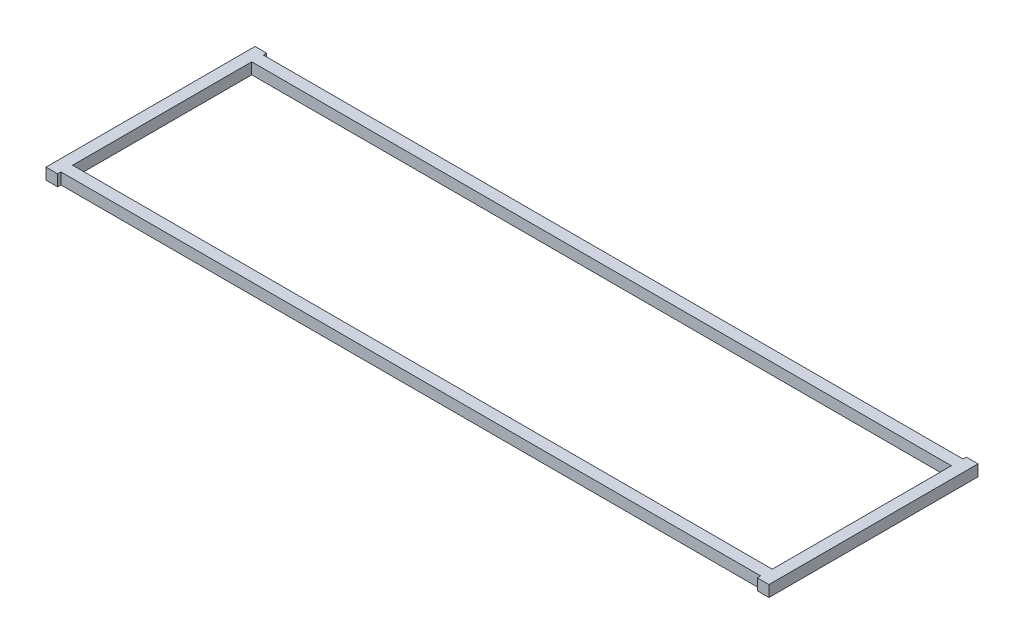
SolidWorks part; units mm, degrees
ref_plane "Front" through (0, 0, 0) normal (0, 0, 1) x (1, 0, 0)
ref_plane "Top" through (0, 0, 0) normal (0, 1, 0) x (1, 0, 0)
ref_plane "Right" through (0, 0, 0) normal (1, 0, 0) x (0, 0, -1)
sketch "Sketch1" plane through (0, 0, 0) normal (0, 1, 0) x (1, 0, 0)
  line L0 (196.85, 58.6835) -> (203.2, 58.6835)
  line L1 (-203.2, 58.6835) -> (-196.85, 58.6835)
  line L2 (-203.2, 58.6835) -> (-203.2, -58.6835)
  line L3 (-203.2, -58.6835) -> (-196.85, -58.6835)
  line L4 (203.2, 58.6835) -> (203.2, -58.6835)
  line L5 (-203.2, 58.6835) -> (203.2, -58.6835) construction
  line L6 (-203.2, -58.6835) -> (203.2, 58.6835) construction
  line L8 (-196.85, 58.6835) -> (-196.85, 56.8196)
  line L9 (-196.85, 56.8196) -> (196.85, 56.8196)
  line L10 (196.85, 58.6835) -> (196.85, 56.8196)
  line L12 (-196.85, -58.6835) -> (-196.85, -56.8196)
  line L13 (-196.85, -56.8196) -> (196.85, -56.8196)
  line L14 (196.85, -58.6835) -> (196.85, -56.8196)
  line L15 (196.85, -58.6835) -> (203.2, -58.6835)
  line L17 (-196.85, -50.4696) -> (196.85, -50.4696)
  line L18 (-196.85, -50.4696) -> (-196.85, 50.4696)
  line L19 (-196.85, 50.4696) -> (196.85, 50.4696)
  line L20 (196.85, -50.4696) -> (196.85, 50.4696)
  line L21 (-196.85, -50.4696) -> (196.85, 50.4696) construction
  line L22 (-196.85, 50.4696) -> (196.85, -50.4696) construction
  point P0 (0, 0)
  point P14 (0, 0)
  dimension "D1" = 406.4
  dimension "D2" = 117.3671
  dimension "D3" = 6.35
  dimension "D4" = 6.35
  dimension "D6" = 6.35
  dimension "D7" = 6.35
  dimension "D5" = 1.8639
extrude "Boss-Extrude1" add sketch "Sketch1" along normal blind 6.35
ref_plane "Plane1" through (0, 6.35, 0) normal (0, 1, 0) x (1, 0, 0)
sketch "Sketch2" plane through (0, 6.35, 0) normal (0, 1, 0) x (1, 0, 0)
  line L24 (196.7484, -58.7851) -> (203.3016, -58.7851)
  line L25 (203.3016, -58.7851) -> (203.3016, 58.7851)
  line L26 (203.3016, 58.7851) -> (196.7484, 58.7851)
  line L27 (196.7484, 58.7851) -> (196.7484, 56.9212)
  line L28 (196.7484, 56.9212) -> (-196.7484, 56.9212)
  line L29 (-196.7484, 56.9212) -> (-196.7484, 58.7851)
  line L30 (-196.7484, 58.7851) -> (-203.3016, 58.7851)
  line L31 (-203.3016, 58.7851) -> (-203.3016, -58.7851)
  line L32 (-203.3016, -58.7851) -> (-196.7484, -58.7851)
  line L33 (-196.7484, -58.7851) -> (-196.7484, -56.9212)
  line L34 (-196.7484, -56.9212) -> (196.7484, -56.9212)
  line L35 (196.7484, -56.9212) -> (196.7484, -58.7851)
  line L36 (196.7484, -58.7851) -> (203.3016, -58.7851)
  line L37 (203.3016, -58.7851) -> (203.3016, 58.7851)
  line L38 (203.3016, 58.7851) -> (196.7484, 58.7851)
  line L39 (196.7484, 58.7851) -> (196.7484, 56.9212)
  line L40 (196.7484, 56.9212) -> (-196.7484, 56.9212)
  line L41 (-196.7484, 56.9212) -> (-196.7484, 58.7851)
  line L42 (-196.7484, 58.7851) -> (-203.3016, 58.7851)
  line L43 (-203.3016, 58.7851) -> (-203.3016, -58.7851)
  line L44 (-203.3016, -58.7851) -> (-196.7484, -58.7851)
  line L45 (-196.7484, -58.7851) -> (-196.7484, -56.9212)
  line L46 (-196.7484, -56.9212) -> (196.7484, -56.9212)
  line L47 (196.7484, -56.9212) -> (196.7484, -58.7851)
  line L50 (196.7484, -50.368) -> (196.7484, 50.368)
  line L51 (-196.7484, -50.368) -> (196.7484, -50.368)
  line L52 (-196.7484, 50.368) -> (-196.7484, -50.368)
  line L53 (196.7484, 50.368) -> (-196.7484, 50.368)
  line L54 (196.7484, -50.368) -> (196.7484, 50.368)
  line L55 (-196.7484, -50.368) -> (196.7484, -50.368)
  line L56 (-196.7484, 50.368) -> (-196.7484, -50.368)
  line L57 (196.7484, 50.368) -> (-196.7484, 50.368)
  dimension "D1" = 0.1016
  dimension "D2" = 0.1016
extrude "Boss-Extrude2" add sketch "Sketch2" against normal blind 6.35
ref_plane "Plane2" [suppressed] through (0, 6.35, 0) normal (0, 1, 0) x (1, 0, 0)
sketch "Sketch3" [suppressed] plane through (0, 6.35, 0) normal (0, 1, 0) x (1, 0, 0)
  line L24 (196.7484, -63.354) -> (203.3016, -63.354)
  line L25 (203.3016, -63.354) -> (203.3016, 63.354)
  line L26 (203.3016, 63.354) -> (196.7484, 63.354)
  line L27 (196.7484, 63.354) -> (196.7484, 61.4901)
  line L28 (196.7484, 61.4901) -> (-196.7484, 61.4901)
  line L29 (-196.7484, 61.4901) -> (-196.7484, 63.354)
  line L30 (-196.7484, 63.354) -> (-203.3016, 63.354)
  line L31 (-203.3016, 63.354) -> (-203.3016, -63.354)
  line L32 (-203.3016, -63.354) -> (-196.7484, -63.354)
  line L33 (-196.7484, -63.354) -> (-196.7484, -61.4901)
  line L34 (-196.7484, -61.4901) -> (196.7484, -61.4901)
  line L35 (196.7484, -61.4901) -> (196.7484, -63.354)
  line L36 (196.7484, -63.354) -> (203.3016, -63.354)
  line L37 (203.3016, -63.354) -> (203.3016, 63.354)
  line L38 (203.3016, 63.354) -> (196.7484, 63.354)
  line L39 (196.7484, 63.354) -> (196.7484, 61.4901)
  line L40 (196.7484, 61.4901) -> (-196.7484, 61.4901)
  line L41 (-196.7484, 61.4901) -> (-196.7484, 63.354)
  line L42 (-196.7484, 63.354) -> (-203.3016, 63.354)
  line L43 (-203.3016, 63.354) -> (-203.3016, -63.354)
  line L44 (-203.3016, -63.354) -> (-196.7484, -63.354)
  line L45 (-196.7484, -63.354) -> (-196.7484, -61.4901)
  line L46 (-196.7484, -61.4901) -> (196.7484, -61.4901)
  line L47 (196.7484, -61.4901) -> (196.7484, -63.354)
  line L50 (196.7484, -54.9369) -> (196.7484, 54.9369)
  line L51 (-196.7484, -54.9369) -> (196.7484, -54.9369)
  line L52 (-196.7484, 54.9369) -> (-196.7484, -54.9369)
  line L53 (196.7484, 54.9369) -> (-196.7484, 54.9369)
  line L54 (196.7484, -54.9369) -> (196.7484, 54.9369)
  line L55 (-196.7484, -54.9369) -> (196.7484, -54.9369)
  line L56 (-196.7484, 54.9369) -> (-196.7484, -54.9369)
  line L57 (196.7484, 54.9369) -> (-196.7484, 54.9369)
  dimension "D1" = 0.1016
  dimension "D2" = 0.1016
extrude "Boss-Extrude3" [suppressed] add sketch "Sketch3" against normal blind 6.35
ref_plane "Plane3" [suppressed] through (0, 6.35, 0) normal (0, 1, 0) x (1, 0, 0)
sketch "Sketch4" [suppressed] plane through (0, 6.35, 0) normal (0, 1, 0) x (1, 0, 0)
  line L24 (196.7484, -67.9228) -> (203.3016, -67.9228)
  line L25 (203.3016, -67.9228) -> (203.3016, 67.9228)
  line L26 (203.3016, 67.9228) -> (196.7484, 67.9228)
  line L27 (196.7484, 67.9228) -> (196.7484, 66.0589)
  line L28 (196.7484, 66.0589) -> (-196.7484, 66.0589)
  line L29 (-196.7484, 66.0589) -> (-196.7484, 67.9228)
  line L30 (-196.7484, 67.9228) -> (-203.3016, 67.9228)
  line L31 (-203.3016, 67.9228) -> (-203.3016, -67.9228)
  line L32 (-203.3016, -67.9228) -> (-196.7484, -67.9228)
  line L33 (-196.7484, -67.9228) -> (-196.7484, -66.0589)
  line L34 (-196.7484, -66.0589) -> (196.7484, -66.0589)
  line L35 (196.7484, -66.0589) -> (196.7484, -67.9228)
  line L36 (196.7484, -67.9228) -> (203.3016, -67.9228)
  line L37 (203.3016, -67.9228) -> (203.3016, 67.9228)
  line L38 (203.3016, 67.9228) -> (196.7484, 67.9228)
  line L39 (196.7484, 67.9228) -> (196.7484, 66.0589)
  line L40 (196.7484, 66.0589) -> (-196.7484, 66.0589)
  line L41 (-196.7484, 66.0589) -> (-196.7484, 67.9228)
  line L42 (-196.7484, 67.9228) -> (-203.3016, 67.9228)
  line L43 (-203.3016, 67.9228) -> (-203.3016, -67.9228)
  line L44 (-203.3016, -67.9228) -> (-196.7484, -67.9228)
  line L45 (-196.7484, -67.9228) -> (-196.7484, -66.0589)
  line L46 (-196.7484, -66.0589) -> (196.7484, -66.0589)
  line L47 (196.7484, -66.0589) -> (196.7484, -67.9228)
  line L50 (196.7484, -59.5057) -> (196.7484, 59.5057)
  line L51 (-196.7484, -59.5057) -> (196.7484, -59.5057)
  line L52 (-196.7484, 59.5057) -> (-196.7484, -59.5057)
  line L53 (196.7484, 59.5057) -> (-196.7484, 59.5057)
  line L54 (196.7484, -59.5057) -> (196.7484, 59.5057)
  line L55 (-196.7484, -59.5057) -> (196.7484, -59.5057)
  line L56 (-196.7484, 59.5057) -> (-196.7484, -59.5057)
  line L57 (196.7484, 59.5057) -> (-196.7484, 59.5057)
  dimension "D1" = 0.1016
  dimension "D2" = 0.1016
extrude "Boss-Extrude4" [suppressed] add sketch "Sketch4" against normal blind 6.35
equation "\"D2@Sketch1\"     = (4.87075-.25)"
